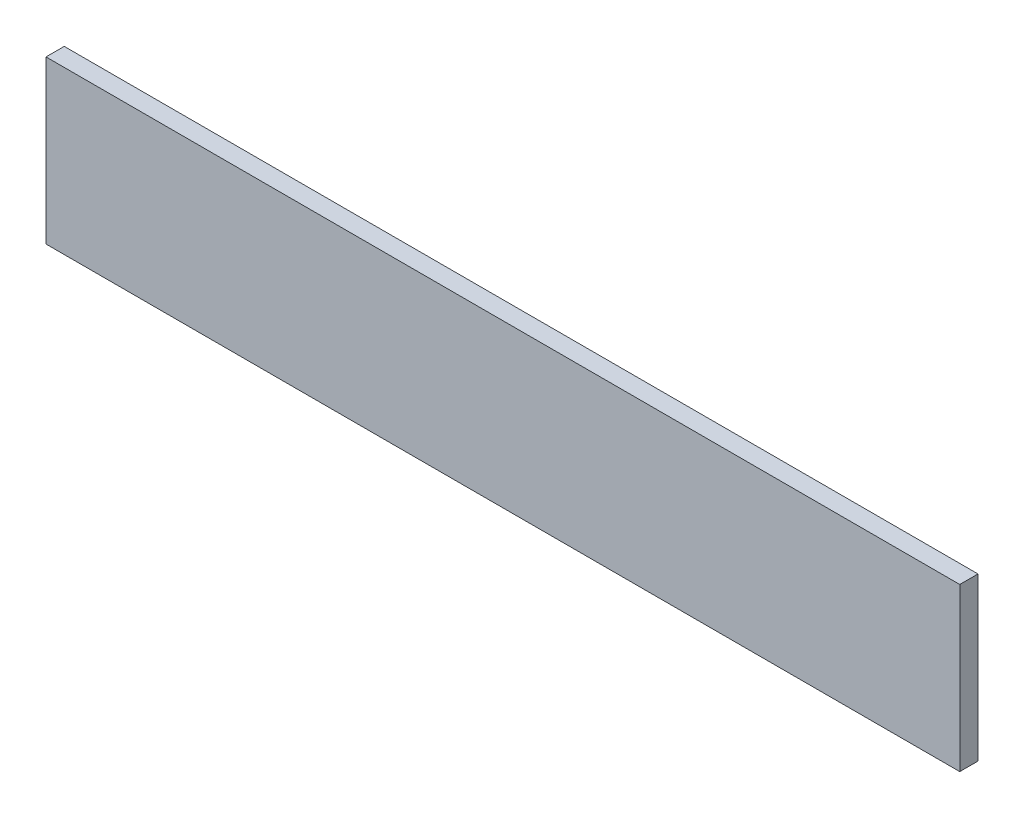
SolidWorks part; units mm, degrees
ref_plane "Płaszczyzna przednia" through (0, 0, 0) normal (0, 0, 1) x (1, 0, 0)
ref_plane "Płaszczyzna górna" through (0, 0, 0) normal (0, 1, 0) x (1, 0, 0)
ref_plane "Płaszczyzna prawa" through (0, 0, 0) normal (1, 0, 0) x (0, 0, -1)
sketch "Szkic1" plane through (0, 0, 0) normal (0, 0, 1) x (1, 0, 0)
  line L1 (0, 0) -> (451, 0)
  line L2 (0, 0) -> (0, 80)
  line L3 (0, 80) -> (451, 80)
  line L4 (451, 0) -> (451, 80)
  dimension "D1" = 451
  dimension "D2" = 80
extrude "Dodanie-wyciągnięcie1" add sketch "Szkic1" against normal blind 9
